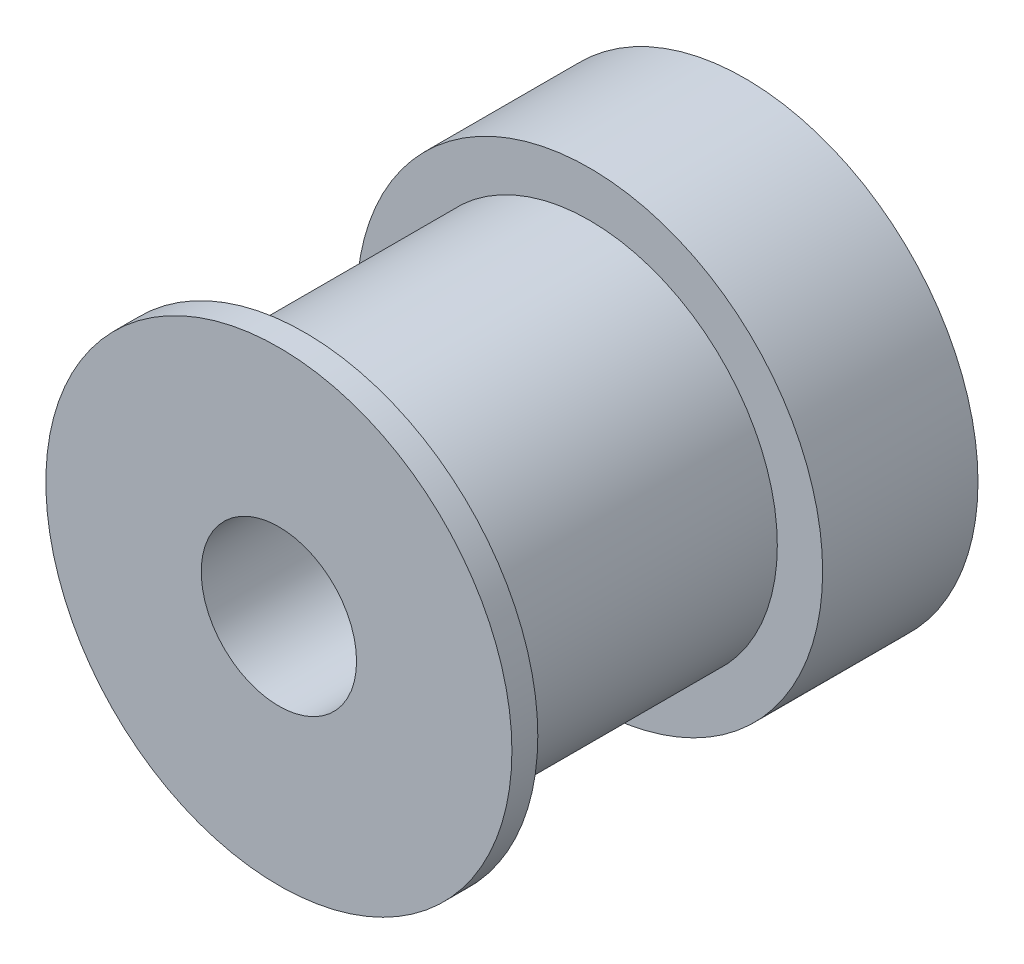
SolidWorks part; units mm, degrees
ref_plane "Front Plane" through (0, 0, 0) normal (0, 0, 1) x (1, 0, 0)
ref_plane "Top Plane" through (0, 0, 0) normal (0, 1, 0) x (1, 0, 0)
ref_plane "Right Plane" through (0, 0, 0) normal (1, 0, 0) x (0, 0, -1)
sketch "Sketch1" plane through (0, 0, 0) normal (0, 0, 1) x (1, 0, 0)
  circle A0 centre (0, 0) radius 3
  circle A1 centre (0, 0) radius 9
  dimension "D1" = 6
  dimension "D2" = 18
extrude "Boss-Extrude1" add sketch "Sketch1" along normal blind 6
sketch "Sketch2" plane through (0, 0, 6) normal (0, 0, 1) x (1, 0, 0)
  circle A0 centre (0, 0) radius 3
  circle A1 centre (0, 0) radius 7.25
  circle A2 centre (0, 0) radius 3 construction
  dimension "D1" = 14.5
extrude "Boss-Extrude2" add sketch "Sketch2" along normal blind 11
sketch "Sketch3" plane through (0, 0, 17) normal (0, 0, 1) x (1, 0, 0)
  circle A0 centre (0, 0) radius 3
  circle A1 centre (0, 0) radius 9
  circle A2 centre (0, 0) radius 3 construction
  dimension "D1" = 18
extrude "Boss-Extrude3" add sketch "Sketch3" along normal blind 1
sketch "Sketch4" plane through (0, 0, 0) normal (0, 1, 0) x (1, 0, 0)
  circle A0 centre (0, -4) radius 1.5
  dimension "D2" = 3
  dimension "D1" = 4
extrude "Cut-Extrude1" cut sketch "Sketch4" against normal through all
